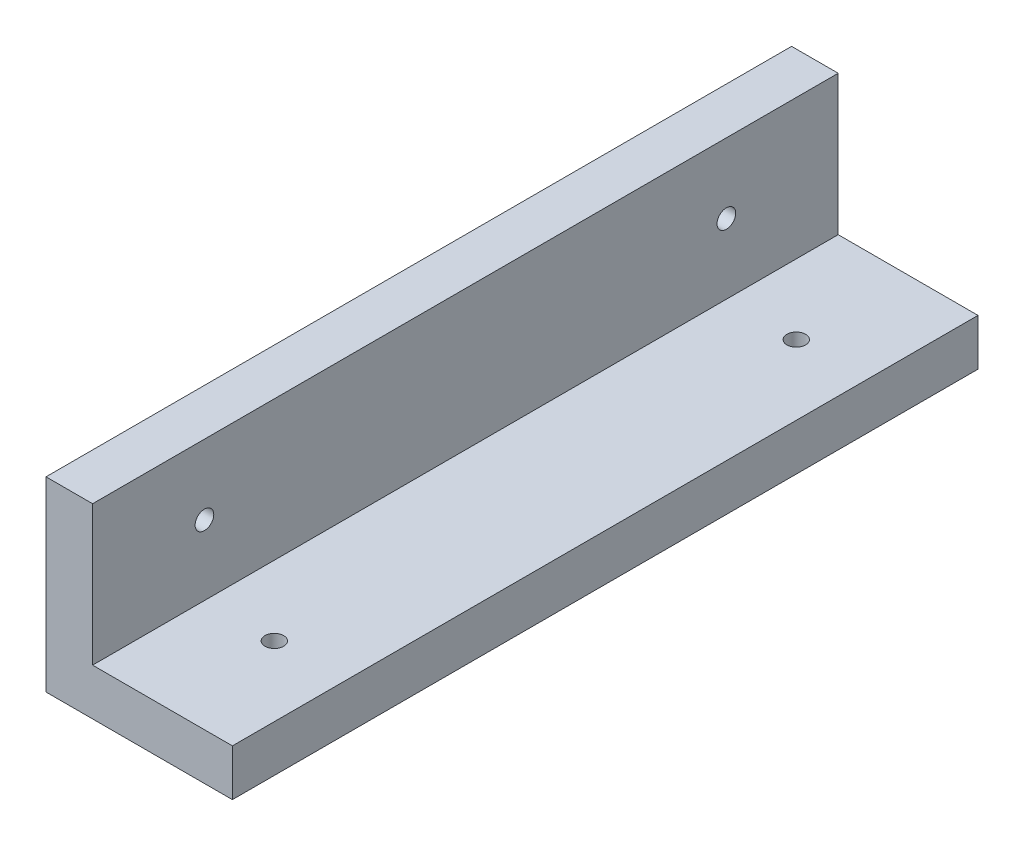
SolidWorks part; units mm, degrees
ref_plane "前基準面" through (0, 0, 0) normal (0, 0, 1) x (1, 0, 0)
ref_plane "上基準面" through (0, 0, 0) normal (0, 1, 0) x (1, 0, 0)
ref_plane "右基準面" through (0, 0, 0) normal (1, 0, 0) x (0, 0, -1)
sketch "草圖1" plane through (0, 0, 0) normal (0, 0, 1) x (1, 0, 0)
  line L0 (-42.4379, 0) -> (50.2032, 0) construction
  line L1 (0, 28.6682) -> (0, -31.7381) construction
  line L2 (0, 0) -> (0, 20)
  line L3 (0, 20) -> (5, 20)
  line L4 (5, 20) -> (5, 5)
  line L5 (5, 5) -> (20, 5)
  line L6 (20, 5) -> (20, 0)
  line L7 (0, 0) -> (20, 0)
  dimension "D1" = 20
  dimension "D2" = 20
  dimension "D3" = 5
  dimension "D4" = 5
extrude "填料-伸長1" add sketch "草圖1" along normal blind 80
sketch "草圖2" plane through (0, 0, 0) normal (0, 1, 0) x (1, 0, 0)
  line L0 (20, -80) -> (20, 0) construction
  line L1 (20, 0) -> (5, 0) construction
  line L2 (20, -80) -> (5, -80) construction
  circle A0 centre (12.5, -12) radius 1
  circle A1 centre (12.5, -68) radius 1
  dimension "D1" = 2
  dimension "D2" = 2
  dimension "D3" = 7.5
  dimension "D4" = 12
  dimension "D5" = 7.5
  dimension "D6" = 12
extrude "除料-伸長2" cut sketch "草圖2" against normal blind 10 and the other way blind 10
sketch "草圖3" plane through (0, 0, 0) normal (1, 0, 0) x (0, 0, -1)
  line L0 (-80, 20) -> (0, 20) construction
  line L1 (0, 20) -> (0, 0) construction
  line L2 (-80, 20) -> (-80, 0) construction
  circle A0 centre (-12, 12.5) radius 1
  circle A1 centre (-68, 12.5) radius 1
  dimension "D1" = 2
  dimension "D2" = 2
  dimension "D3" = 7.5
  dimension "D4" = 12
  dimension "D5" = 7.5
  dimension "D6" = 12
extrude "除料-伸長3" cut sketch "草圖3" against normal blind 10 and the other way blind 10
